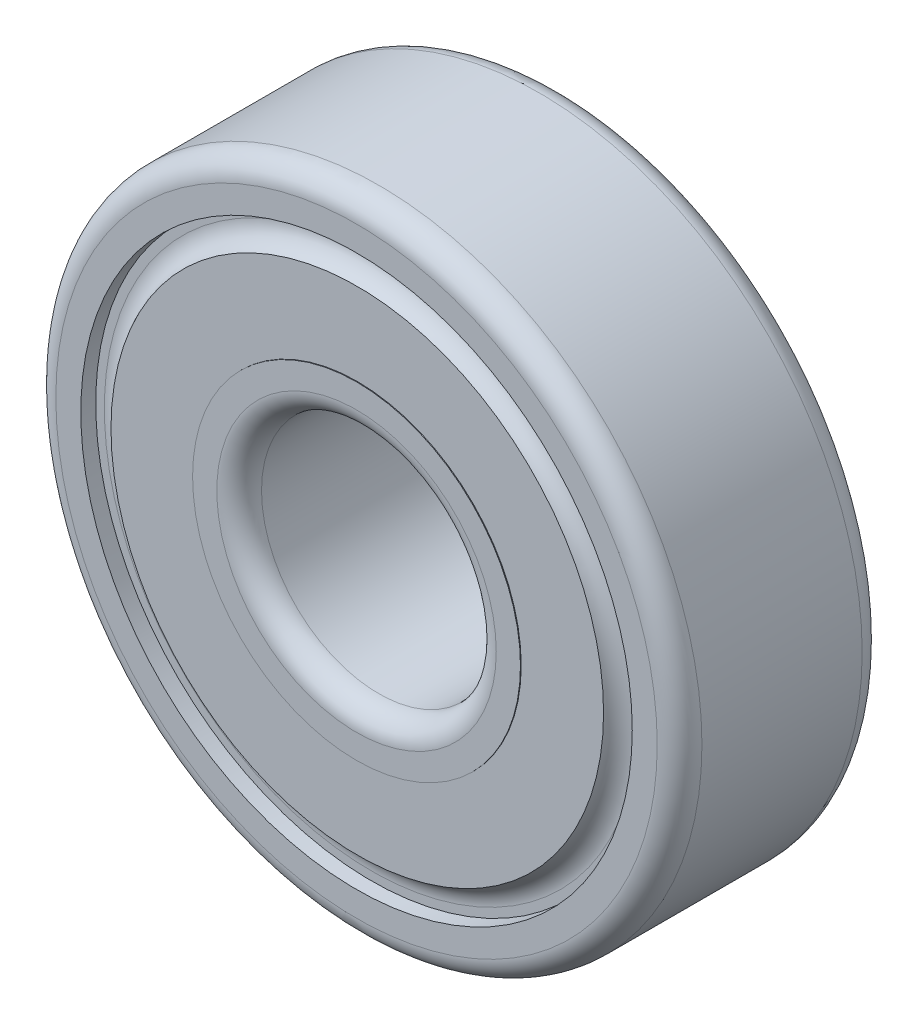
SolidWorks part; units mm, degrees
ref_plane "Front Plane" through (0, 0, 0) normal (0, 0, 1) x (1, 0, 0)
ref_plane "Top Plane" through (0, 0, 0) normal (0, 1, 0) x (1, 0, 0)
ref_plane "Right Plane" through (0, 0, 0) normal (1, 0, 0) x (0, 0, -1)
sketch "Sketch1" plane through (0, 0, 0) normal (0, 1, 0) x (1, 0, 0)
  line L0 (4.0005, 2.7305) -> (4.0005, -2.7305)
  line L1 (4.7625, -3.4925) -> (5.588, -3.4925)
  line L2 (5.588, -3.4925) -> (5.588, -3.4671)
  line L3 (5.588, -3.4671) -> (8.3947, -3.4671)
  line L4 (9.1036, -2.9845) -> (9.398, -2.9845)
  line L5 (9.398, -2.9845) -> (9.398, -3.4925)
  line L6 (9.398, -3.4925) -> (10.2489, -3.4925)
  line L7 (11.0109, -2.7305) -> (11.0109, 2.7305)
  line L8 (10.2489, 3.4925) -> (9.398, 3.4925)
  line L9 (9.398, 3.4925) -> (9.398, 2.9845)
  line L10 (9.398, 2.9845) -> (8.3947, 2.9845)
  line L11 (8.3947, 2.9845) -> (8.3947, 3.4671)
  line L12 (8.3947, 3.4671) -> (5.588, 3.4671)
  line L13 (5.588, 3.4671) -> (5.588, 3.4925)
  line L14 (5.588, 3.4925) -> (4.7625, 3.4925)
  line L15 (0, 3.4953) -> (0, -3.4962) construction
  arc A0 (4.7625, 3.4925) -> (4.0005, 2.7305) centre (4.7625, 2.7305) ccw
  arc A1 (4.0005, -2.7305) -> (4.7625, -3.4925) centre (4.7625, -2.7305) ccw
  arc A2 (8.3947, -3.4671) -> (9.1036, -2.9845) centre (9.1036, -3.7465) cw
  arc A3 (10.2489, -3.4925) -> (11.0109, -2.7305) centre (10.2489, -2.7305) ccw
  arc A4 (11.0109, 2.7305) -> (10.2489, 3.4925) centre (10.2489, 2.7305) ccw
revolve "Revolve1" add sketch "Sketch1" angle 360 about L15
